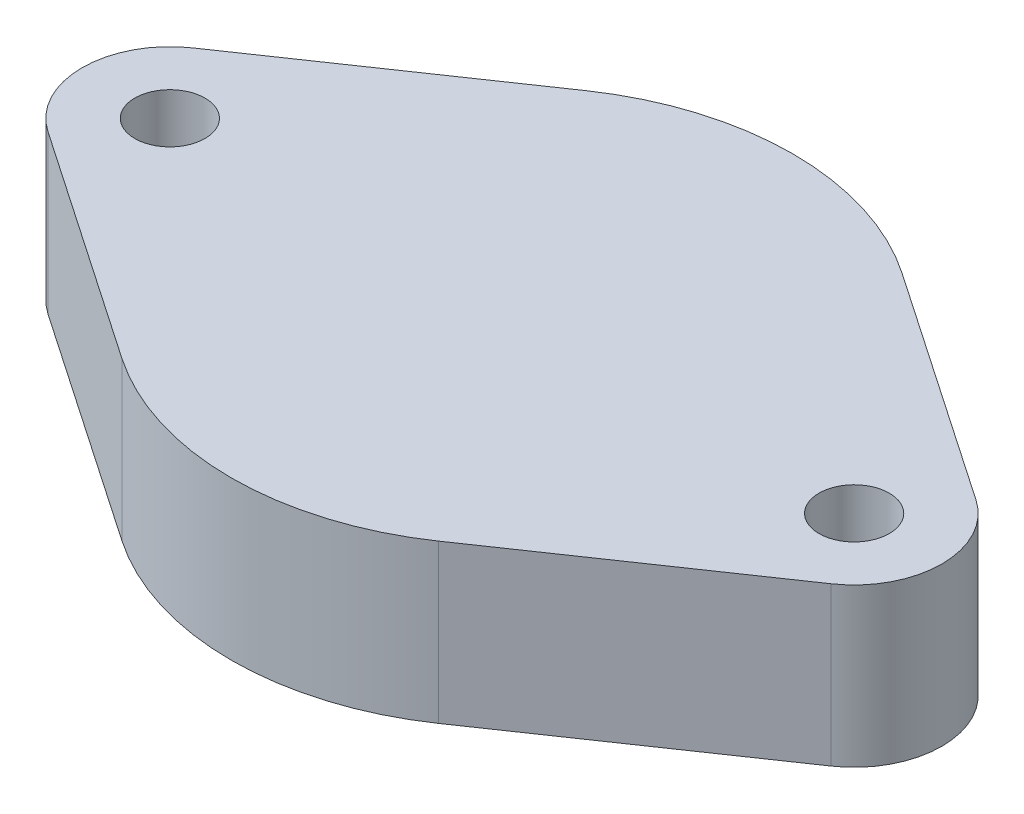
SolidWorks part; units mm, degrees
ref_plane "前基準面" through (0, 0, 0) normal (0, 0, 1) x (1, 0, 0)
ref_plane "上基準面" through (0, 0, 0) normal (0, 1, 0) x (1, 0, 0)
ref_plane "右基準面" through (0, 0, 0) normal (1, 0, 0) x (0, 0, -1)
sketch "草圖1" plane through (0, 0, 0) normal (0, 1, 0) x (1, 0, 0)
  line L0 (-19.5, 0) -> (19.5, 0) construction
  line L1 (-22.3205, 4.1285) -> (-9.0256, 13.2113)
  line L2 (9.0256, 13.2113) -> (22.3205, 4.1285)
  line L3 (22.3205, -4.1285) -> (9.0256, -13.2113)
  line L4 (-9.0256, -13.2113) -> (-22.3205, -4.1285)
  circle A0 centre (19.5, 0) radius 2
  circle A1 centre (-19.5, 0) radius 2
  arc A2 (-9.0256, 13.2113) -> (9.0256, 13.2113) centre (0, 0) cw
  arc A3 (22.3205, 4.1285) -> (22.3205, -4.1285) centre (19.5, 0) cw
  arc A4 (9.0256, -13.2113) -> (-9.0256, -13.2113) centre (0, 0) cw
  arc A5 (-22.3205, -4.1285) -> (-22.3205, 4.1285) centre (-19.5, 0) cw
  point P9 (-18.9739, 0)
  point P15 (0, 0)
  point P17 (19.5, -0.5877)
  point P18 (0, -2.8395)
  point P19 (2.3528, 0.8554)
  point P20 (0.5518, 0.3554)
  point P21 (0, 0)
  dimension "D2" = 4
  dimension "D3" = 5
  dimension "D4" = 5
  dimension "D5" = 16
  dimension "D6" = 16
  dimension "D1" = 39
extrude "填料-伸長1" add sketch "草圖1" along normal blind 9
